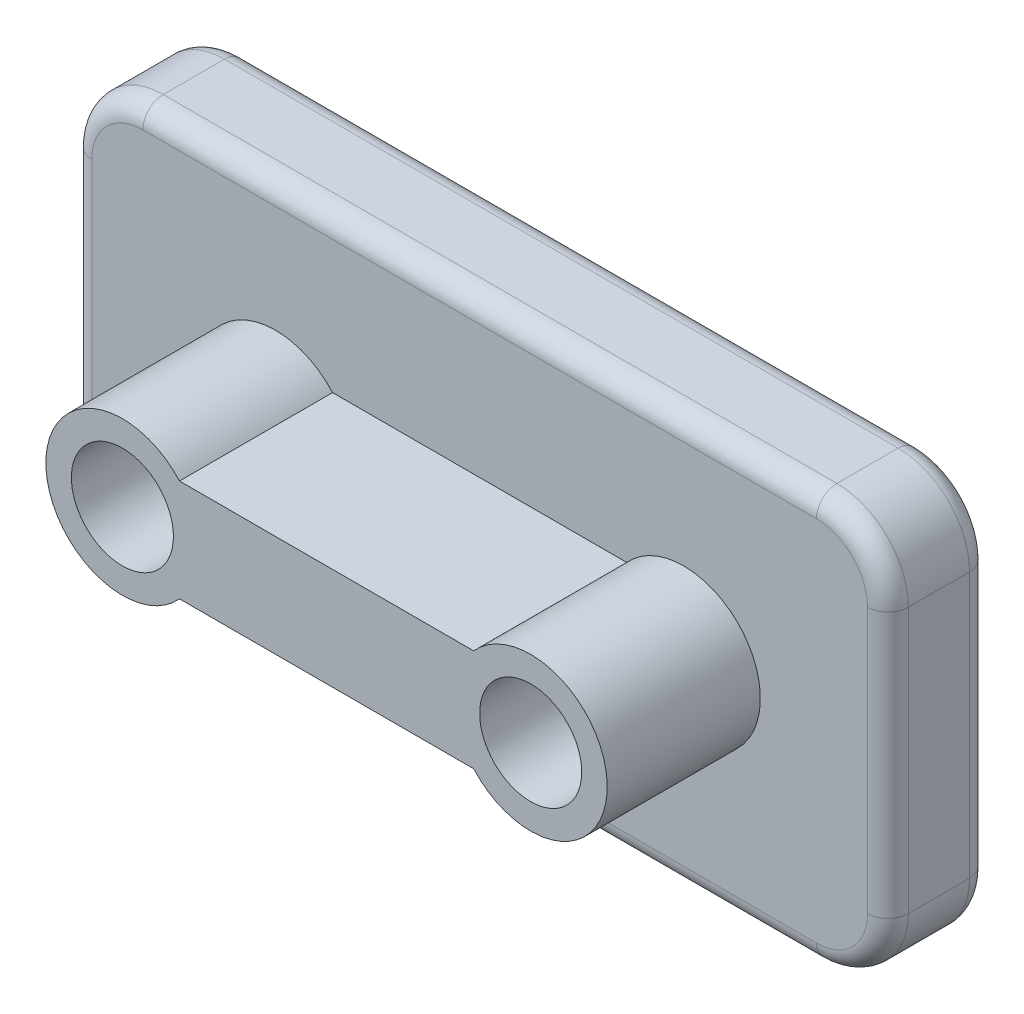
SolidWorks part; units mm, degrees
ref_plane "Front Plane" through (0, 0, 0) normal (0, 0, 1) x (1, 0, 0)
ref_plane "Top Plane" through (0, 0, 0) normal (0, 1, 0) x (1, 0, 0)
ref_plane "Right Plane" through (0, 0, 0) normal (1, 0, 0) x (0, 0, -1)
sketch "Sketch1" plane through (0, 0, 0) normal (0, 0, 1) x (1, 0, 0)
  line L1 (7, 0) -> (73, 0)
  line L2 (0, 7) -> (0, 33)
  line L3 (7, 40) -> (73, 40)
  line L4 (80, 7) -> (80, 33)
  arc A0 (73, 40) -> (80, 33) centre (73, 33) cw
  arc A1 (73, 0) -> (80, 7) centre (73, 7) ccw
  arc A2 (7, 0) -> (0, 7) centre (7, 7) cw
  arc A3 (0, 33) -> (7, 40) centre (7, 33) cw
  point P7 (80, 40)
  point P12 (0, 0)
  point P15 (0, 40)
  dimension "D3" = 7
  dimension "D1" = 80
  dimension "D2" = 40
extrude "Boss-Extrude1" add sketch "Sketch1" along normal blind 10 contours L2 A3 L3 A0 L4 A1 L1 A2
fillet "Fillet1" radius 2 8 edges at (40, 0, 0) (77.9497, 2.0503, 0) (80, 20, 0) (77.9497, 37.9497, 0) (40, 40, 0) (2.0503, 37.9497, 0) (0, 20, 0) (2.0503, 2.0503, 0)
fillet "Fillet2" radius 2 8 edges at (0, 20, 10) (2.0503, 37.9497, 10) (40, 40, 10) (77.9497, 37.9497, 10) (80, 20, 10) (77.9497, 2.0503, 10) (40, 0, 10) (2.0503, 2.0503, 10)
sketch "Sketch2" plane through (0, 0, 10) normal (0, 0, 1) x (1, 0, 0)
  line L0 (2, 33) -> (2, 7) construction
  circle A2 centre (20, 20) radius 7.5
  circle A3 centre (60, 20) radius 7.5
  point P10 (2, 20)
  dimension "D4" = 15
  dimension "D1" = 40
  dimension "D2" = 18
extrude "Boss-Extrude3" add sketch "Sketch2" along normal blind 15
sketch "Sketch3" plane through (0, 0, 25) normal (0, 0, 1) x (1, 0, 0)
  circle A0 centre (20, 20) radius 5
extrude "Cut-Extrude1" cut sketch "Sketch3" against normal up to surface (15 mm away) up to face at (12.5, 20, 10)
sketch "Sketch4" plane through (0, 0, 25) normal (0, 0, 1) x (1, 0, 0)
  circle A0 centre (60, 20) radius 5
extrude "Cut-Extrude2" cut sketch "Sketch4" against normal up to surface (15 mm away) up to face at (12.5, 20, 10)
sketch "Sketch5" plane through (0, 0, 25) normal (0, 0, 1) x (1, 0, 0)
  line L0 (48.4361, 20) -> (33.4361, 20)
rib "Rib1" sketch "Sketch5" sketch "Sketch5" thickness 10 extrusion direction normal to sketch draft on no parameters "D1"=10
